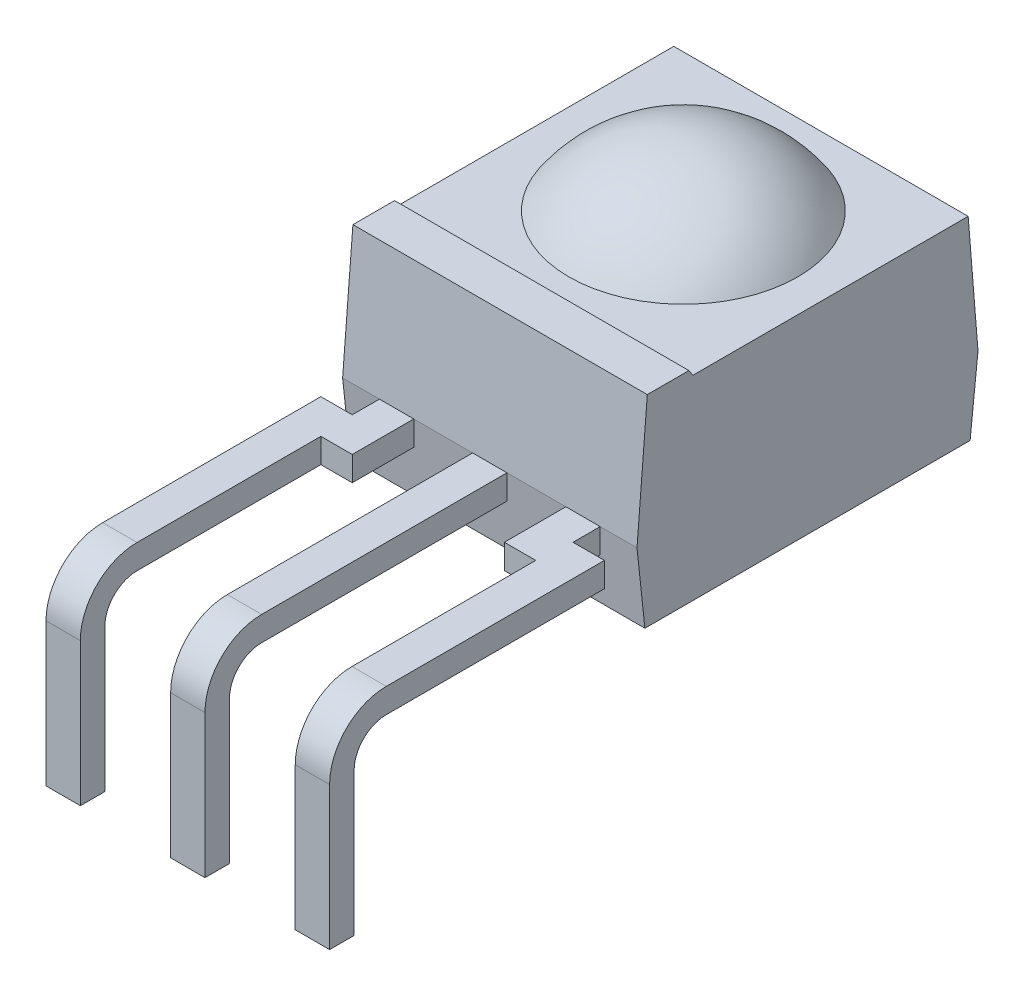
SolidWorks part; units mm, degrees
ref_plane "Front Plane" through (0, 0, 0) normal (0, 0, 1) x (1, 0, 0)
ref_plane "Top Plane" through (0, 0, 0) normal (0, 1, 0) x (1, 0, 0)
ref_plane "Right Plane" through (0, 0, 0) normal (1, 0, 0) x (0, 0, -1)
sketch "Sketch1" plane through (0, 0, 0) normal (0, 1, 0) x (1, 0, 0)
  line L1 (-3, 3.475) -> (3, 3.475)
  line L2 (-3, 3.475) -> (-3, -3.475)
  line L3 (-3, -3.475) -> (3, -3.475)
  line L4 (3, 3.475) -> (3, -3.475)
  line L5 (-3, 3.475) -> (3, -3.475) construction
  line L6 (-3, -3.475) -> (3, 3.475) construction
  point P0 (0, 0)
  dimension "D1" = 6
  dimension "D2" = 6.95
extrude "Boss-Extrude1" add sketch "Sketch1" along normal blind 4.1
sketch "Sketch2" plane through (-3, 0, 0) normal (-1, 0, 0) x (0, 0, 1)
  line L0 (-3.475, 1.5) -> (3.475, 1.5) construction
  line L1 (-3.475, 4.1) -> (-3.475, 0) construction
  line L2 (3.475, 4.1) -> (3.475, 0) construction
  line L3 (-3.475, 0) -> (3.475, 0) construction
  line L4 (-3.475, 1.5) -> (-3.2749, 3.9766)
  line L5 (-3.2488, 4.2994) -> (-4.0867, 4.2994)
  line L6 (-4.0867, 4.2994) -> (-4.0867, -0.6115)
  line L7 (-4.0867, -0.6115) -> (-3.2488, -0.6115)
  line L8 (-3.2488, -0.6115) -> (-3.475, 1.5)
  line L9 (0, 0) -> (0, 4.1) construction
  line L10 (-3.475, 4.1) -> (3.475, 4.1) construction
  line L11 (3.2488, -0.6115) -> (3.475, 1.5)
  line L12 (4.0867, -0.6115) -> (3.2488, -0.6115)
  line L13 (4.0867, 4.2994) -> (4.0867, -0.6115)
  line L14 (3.2488, 4.2994) -> (4.0867, 4.2994)
  line L15 (3.475, 1.5) -> (3.2488, 4.2994)
  line L16 (2.5482, 4.2994) -> (2.3353, 3.9766)
  line L17 (2.3353, 3.9766) -> (-3.2749, 3.9766)
  line L19 (2.5482, 4.2994) -> (-3.2488, 4.2994)
  dimension "D1" = 1.5
extrude "Cut-Extrude2" cut sketch "Sketch2" against normal blind 10
sketch "Sketch5" plane through (0, 0, 0) normal (1, 0, 0) x (0, 0, -1)
  line L0 (3.2749, 3.9766) -> (-2.3353, 3.9766) construction
  line L1 (0.4698, 3.9766) -> (0.4698, 3.4416) construction
  line L2 (0.4698, 5.2162) -> (0.4698, 3.9766)
  line L3 (0.4698, 3.9766) -> (2.8034, 3.9766)
  arc A0 (0.4698, 5.2162) -> (2.8034, 3.9766) centre (0.4698, 2.3997) cw
revolve "Revolve2" add sketch "Sketch5" angle 360 about L1
ref_plane "Plane2" through (0, 1.5, 0) normal (0, 1, 0) x (1, 0, 0)
sketch "Sketch6" plane through (0, 1.5, 0) normal (0, 1, 0) x (1, 0, 0)
  line L0 (3, -3.475) -> (-3, -3.475) construction
  line L1 (-0.35, -3.475) -> (0.35, -3.475)
  line L2 (-0.35, -3.475) -> (-0.35, -8.475)
  line L3 (-0.35, -8.475) -> (0.35, -8.475)
  line L4 (0.35, -3.475) -> (0.35, -8.475)
  line L5 (-0.35, -3.475) -> (0.35, -8.475) construction
  line L6 (-0.35, -8.475) -> (0.35, -3.475) construction
  line L7 (0, -3.475) -> (0, -8.475) construction
  line L8 (-1.55, -3.475) -> (-1.55, -4.7285)
  line L9 (-1.55, -4.7285) -> (-2.19, -4.7285)
  line L10 (-2.19, -4.7285) -> (-2.19, -8.475)
  line L11 (-2.19, -8.475) -> (-2.89, -8.475)
  line L12 (-2.89, -8.475) -> (-2.89, -4.0285)
  line L13 (-2.89, -4.0285) -> (-2.25, -4.0285)
  line L14 (-2.25, -4.0285) -> (-2.25, -3.475)
  line L15 (-2.25, -3.475) -> (-1.55, -3.475)
  line L16 (-2.54, -8.475) -> (-2.54, -4.0285) construction
  line L17 (2.89, -4.0285) -> (2.25, -4.0285)
  line L18 (2.89, -8.475) -> (2.89, -4.0285)
  line L19 (2.19, -8.475) -> (2.89, -8.475)
  line L20 (2.19, -4.7285) -> (2.19, -8.475)
  line L21 (1.55, -4.7285) -> (2.19, -4.7285)
  line L22 (1.55, -3.475) -> (1.55, -4.7285)
  line L23 (2.25, -3.475) -> (1.55, -3.475)
  line L24 (2.25, -4.0285) -> (2.25, -3.475)
  point P0 (0, -5.975)
  dimension "D1" = 5
  dimension "D2" = 0.7
  dimension "D3" = 0.7
  dimension "D4" = 0.7
  dimension "D5" = 0.7
  dimension "D6" = 2.54
  dimension "D7" = 1.2
  dimension "D8" = 1.2535
extrude "Boss-Extrude2" add sketch "Sketch6" against normal blind 0.5 separate body
sketch "Sketch7" plane through (0, 0, 0) normal (1, 0, 0) x (0, 0, -1)
  line L0 (-8.475, 1.25) -> (-4.0285, 1.25) construction
  line L1 (-8.475, 1) -> (-8.475, 1.5) construction
  line L2 (-4.0285, 1) -> (-4.0285, 1.5) construction
  line L3 (-9.3804, 0.3446) -> (-9.3804, -2.5696)
  arc A0 (-8.475, 1.25) -> (-9.3804, 0.3446) centre (-8.475, 0.3446) ccw
sketch "Sketch8" plane through (0, 0, 8.475) normal (0, 0, 1) x (1, 0, 0)
  line L8 (0.35, 1.5) -> (-0.35, 1.5)
  line L9 (-0.35, 1.5) -> (-0.35, 1)
  line L10 (-0.35, 1) -> (0.35, 1)
  line L11 (0.35, 1) -> (0.35, 1.5)
  line L12 (0.35, 1.5) -> (-0.35, 1.5)
  line L13 (-0.35, 1.5) -> (-0.35, 1)
  line L14 (-0.35, 1) -> (0.35, 1)
  line L15 (0.35, 1) -> (0.35, 1.5)
  dimension "D1" = 0
sweep "Sweep1" add profiles "Sketch8" path "Sketch7"
pattern_linear "LPattern1" count 2 spacing 2.54 along (1, 0, 0) of "Sweep1"
pattern_linear "LPattern2" count 2 spacing 2.54 along (-1, 0, 0) of "Sweep1"
